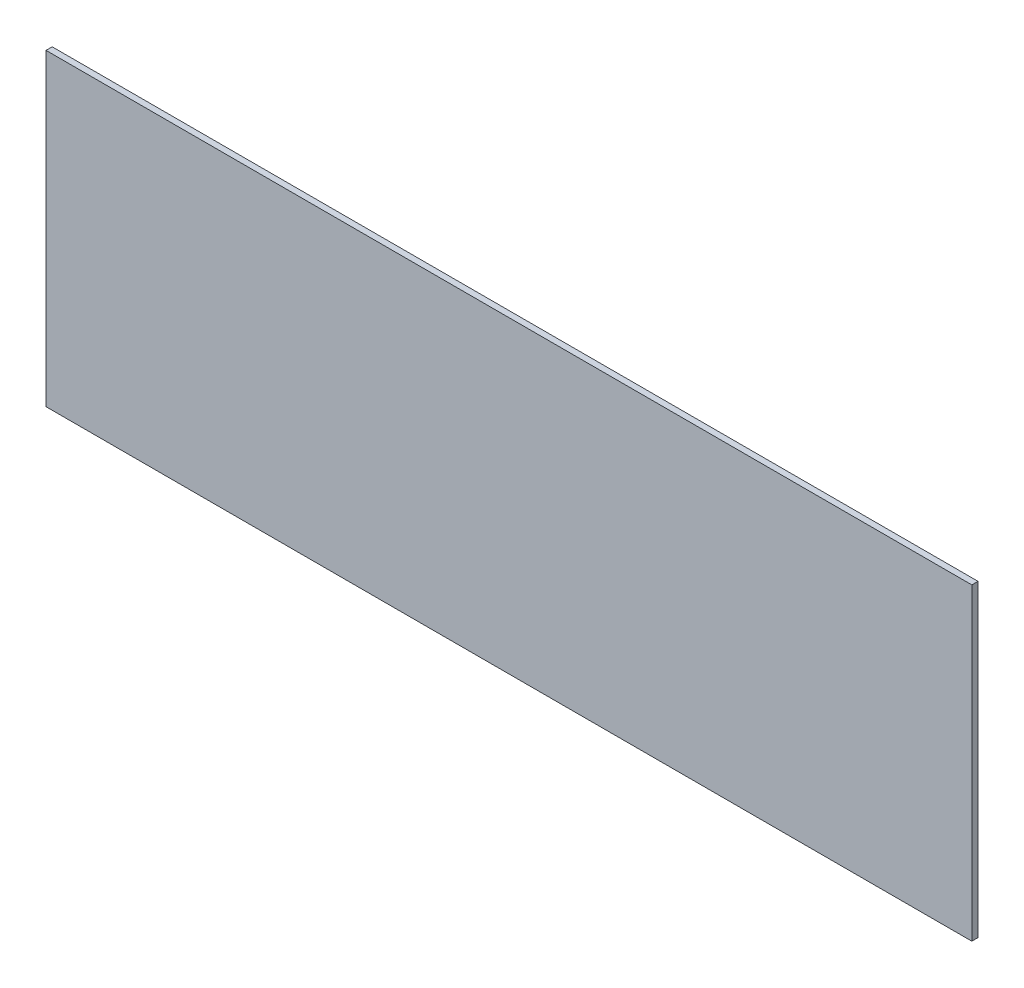
SolidWorks part; units mm, degrees
material "Balsa"
ref_plane "Front Plane" through (0, 0, 0) normal (0, 0, 1) x (1, 0, 0)
ref_plane "Top Plane" through (0, 0, 0) normal (0, 1, 0) x (1, 0, 0)
ref_plane "Right Plane" through (0, 0, 0) normal (1, 0, 0) x (0, 0, -1)
sketch "Sketch1" plane through (0, 0, 0) normal (0, 0, 1) x (1, 0, 0)
  line L1 (600, 200) -> (0, 200)
  line L2 (600, 200) -> (600, 0)
  line L3 (600, 0) -> (0, 0)
  line L4 (0, 200) -> (0, 0)
  dimension "D1" = 600
  dimension "D2" = 200
extrude "Boss-Extrude1" add sketch "Sketch1" along normal blind 4
